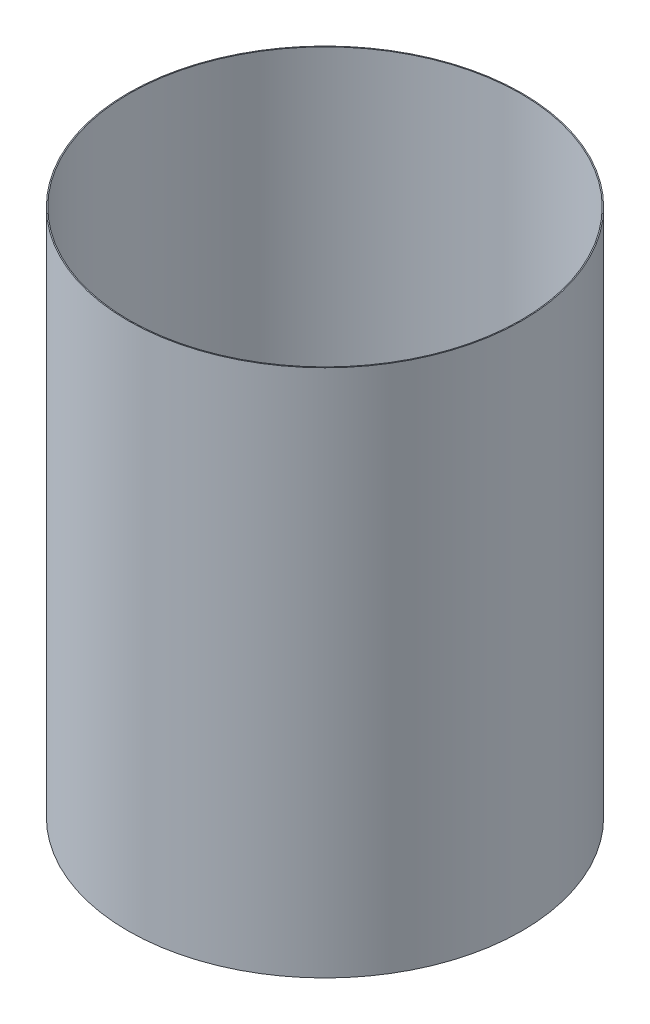
SolidWorks part; units mm, degrees
material "Thornel Mat VMA"
ref_plane "Front Plane" through (0, 0, 0) normal (0, 0, 1) x (1, 0, 0)
ref_plane "Top Plane" through (0, 0, 0) normal (0, 1, 0) x (1, 0, 0)
ref_plane "Right Plane" through (0, 0, 0) normal (1, 0, 0) x (0, 0, -1)
ref_axis "Axis1" through (0, 55, 0) along (0, -1, 0)
sketch "Sketch1" plane through (0, 0, 0) normal (0, 0, 1) x (1, 0, 0)
  line L0 (-49.4665, -19.9059) -> (-49.4665, -153.2559)
  line L2 (-38.1, -19.9059) -> (0, -19.9059) construction
  line L3 (-38.1, -153.2559) -> (0, -153.2559) construction
revolve "Revolve-Thin1" add sketch "Sketch1" angle 360 about axis through (0, 55, 0) along (0, -1, 0)
equation "\"D3@Revolve-Thin1\"=\"CF THICKNESS@Cryo Tank.Assembly\""
